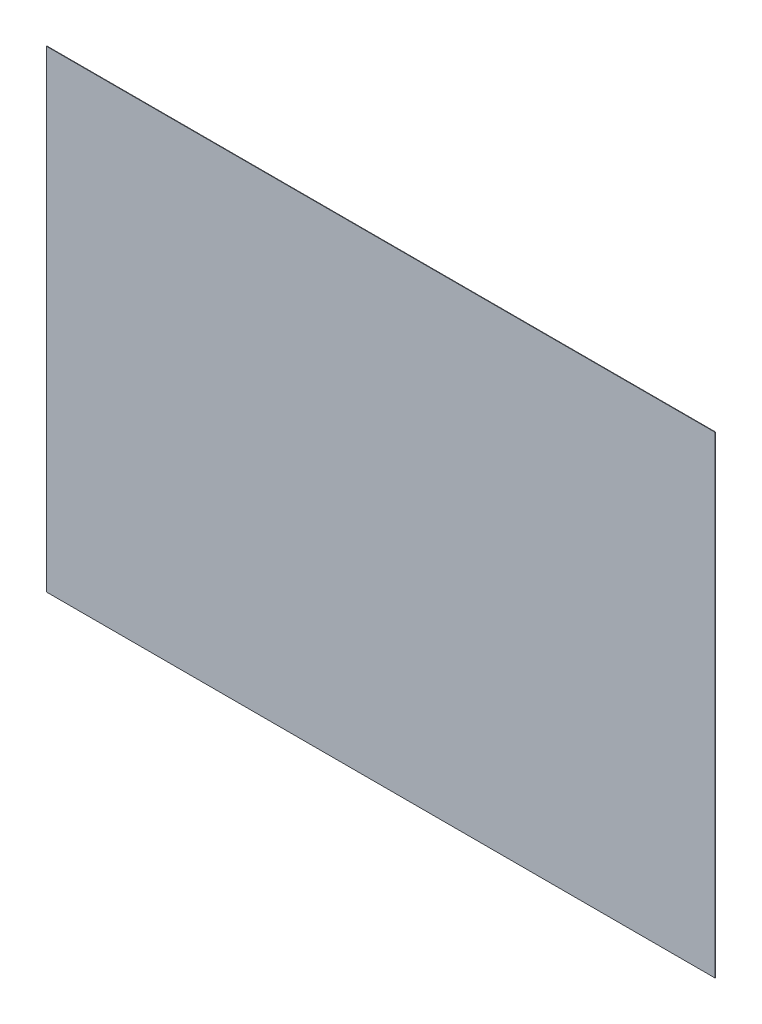
SolidWorks part; units mm, degrees
ref_plane "Front Plane" through (0, 0, 0) normal (0, 0, 1) x (1, 0, 0)
ref_plane "Top Plane" through (0, 0, 0) normal (0, 1, 0) x (1, 0, 0)
ref_plane "Right Plane" through (0, 0, 0) normal (1, 0, 0) x (0, 0, -1)
sketch "Sketch1" plane through (0, 0, 0) normal (0, 0, 1) x (1, 0, 0)
  line L1 (210, -148.5) -> (-210, -148.5)
  line L2 (210, -148.5) -> (210, 148.5)
  line L3 (210, 148.5) -> (-210, 148.5)
  line L4 (-210, -148.5) -> (-210, 148.5)
  line L5 (210, -148.5) -> (-210, 148.5) construction
  line L6 (210, 148.5) -> (-210, -148.5) construction
  point P0 (0, 0)
  dimension "D1" = 297
  dimension "D2" = 420
extrude "Boss-Extrude1" add sketch "Sketch1" along normal blind 0.3
